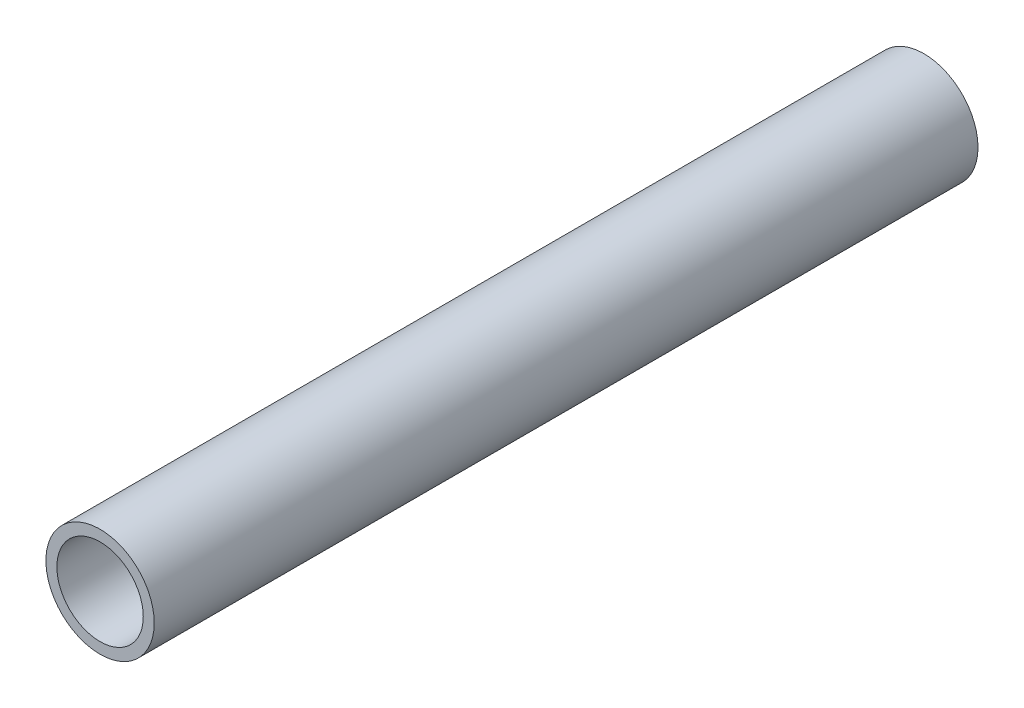
SolidWorks part; units mm, degrees
ref_plane "Front Plane" through (0, 0, 0) normal (0, 0, 1) x (1, 0, 0)
ref_plane "Top Plane" through (0, 0, 0) normal (0, 1, 0) x (1, 0, 0)
ref_plane "Right Plane" through (0, 0, 0) normal (1, 0, 0) x (0, 0, -1)
sketch "Sketch1" plane through (0, 0, 0) normal (0, 0, 1) x (1, 0, 0)
  circle A0 centre (0, 0) radius 16.7005
  dimension "Pipe OD" = 33.401
extrude "Extrude-Thin1" add sketch "Sketch1" along normal mid plane 254 thin thin type one direction reverse wall 3.3782
